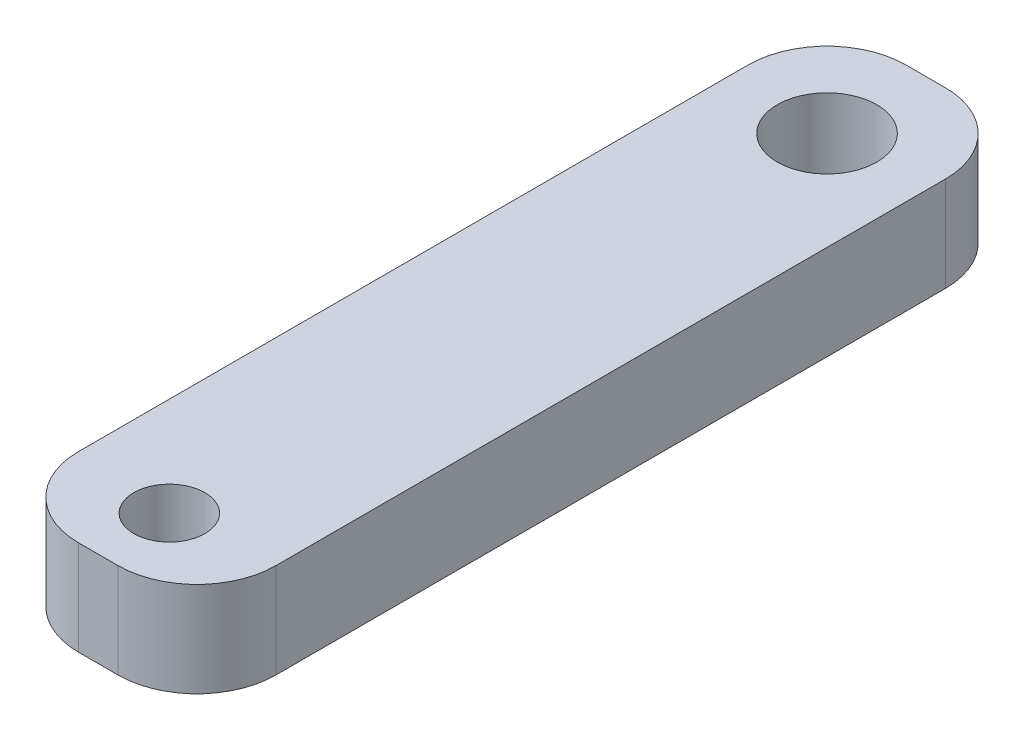
SolidWorks part; units mm, degrees
ref_plane "Front Plane" through (0, 0, 0) normal (0, 0, 1) x (1, 0, 0)
ref_plane "Top Plane" through (0, 0, 0) normal (0, 1, 0) x (1, 0, 0)
ref_plane "Right Plane" through (0, 0, 0) normal (1, 0, 0) x (0, 0, -1)
sketch "Sketch1" plane through (0, 80.955, 0) normal (0, 1, 0) x (1, 0, 0)
  line L0 (101.4051, -119.0901) -> (101.4051, -200.916) construction
  line L1 (186.8171, -176.8525) -> (50.888, -176.8525) construction
  line L2 (142.4379, -152.5253) -> (143.7079, -152.5253)
  line L3 (139.8979, -155.0653) -> (139.8979, -176.5985)
  line L4 (142.4379, -179.1385) -> (143.7079, -179.1385)
  line L5 (146.2479, -155.0653) -> (146.2479, -176.5985)
  line L6 (139.8979, -152.5253) -> (146.2479, -179.1385) construction
  line L7 (139.8979, -179.1385) -> (146.2479, -152.5253) construction
  arc A0 (119.797, -135.593) -> (83.0132, -135.593) centre (101.4051, -137.5901) ccw construction
  circle A1 centre (143.0729, -155.7003) radius 1.6
  circle A2 centre (143.0729, -155.7003) radius 1.6 construction
  circle A3 centre (143.0729, -176.8525) radius 1.143
  arc A4 (143.7079, -179.1385) -> (146.2479, -176.5985) centre (143.7079, -176.5985) ccw
  arc A5 (139.8979, -176.5985) -> (142.4379, -179.1385) centre (142.4379, -176.5985) ccw
  arc A6 (142.4379, -152.5253) -> (139.8979, -155.0653) centre (142.4379, -155.0653) ccw
  arc A7 (143.7079, -152.5253) -> (146.2479, -155.0653) centre (143.7079, -155.0653) cw
  point P10 (143.0729, -165.8319)
  point P16 (143.0729, -152.5253)
  point P20 (0, 0)
  dimension "D3" = 2.286
  dimension "D4" = 2.286
  dimension "D5" = 2.54
  dimension "D1" = 6.35
  dimension "D2" = 3.175
extrude "Boss-Extrude1" add sketch "Sketch1" along normal blind 3.048
